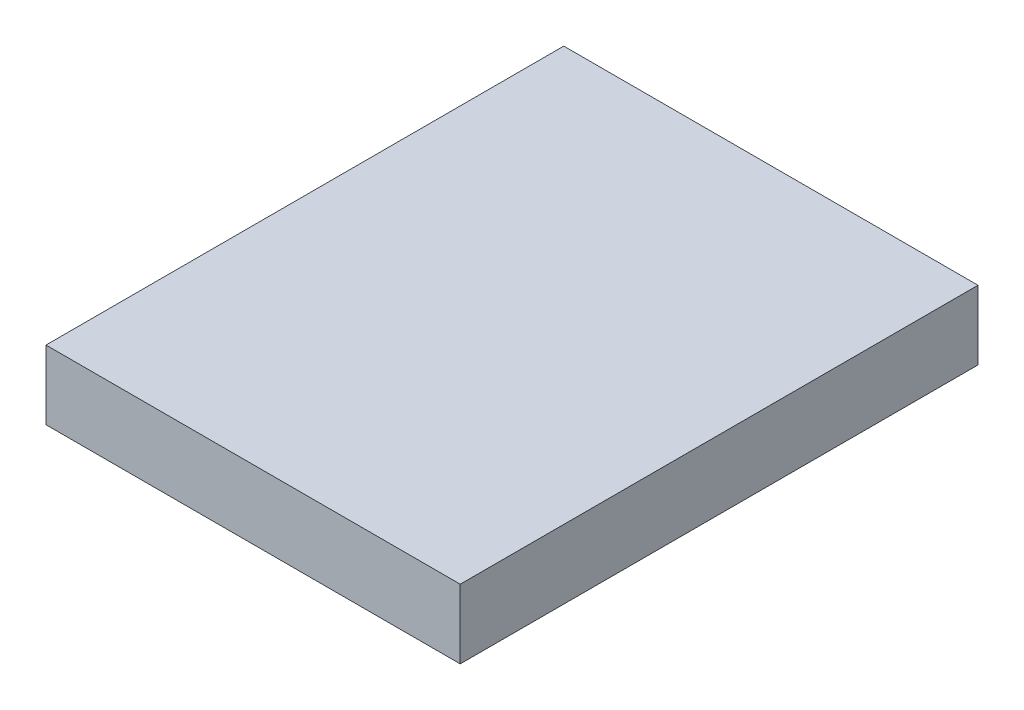
SolidWorks part; units mm, degrees
ref_plane "Front Plane" through (0, 0, 0) normal (0, 0, 1) x (1, 0, 0)
ref_plane "Top Plane" through (0, 0, 0) normal (0, 1, 0) x (1, 0, 0)
ref_plane "Right Plane" through (0, 0, 0) normal (1, 0, 0) x (0, 0, -1)
sketch "Sketch1" plane through (0, 0, 0) normal (0, 1, 0) x (1, 0, 0)
  line L1 (0, 0) -> (229, 0)
  line L2 (0, 0) -> (0, -12.7)
  line L3 (0, -12.7) -> (229, -12.7)
  line L4 (229, 0) -> (229, -12.7)
  dimension "D1" = 229
  dimension "D2" = 12.7
extrude "Boss-Extrude1" add sketch "Sketch1" against normal blind 1
sketch "Sketch2" [suppressed] plane through (0, 0, 0) normal (0, 1, 0) x (1, 0, 0)
  line L0 (229, -12.7) -> (229, 0) construction
  line L1 (0, -12.7) -> (229, -12.7)
  line L2 (0, -12.7) -> (0, -6)
  line L3 (0, -6) -> (229, -6)
  line L4 (229, -12.7) -> (229, -6)
  line L5 (229, 0) -> (0, 0) construction
  dimension "D1" = 6
extrude "Cut-Extrude1" [suppressed] cut sketch "Sketch2" against normal through all
sketch "Sketch3" [suppressed] plane through (0, 0, 0) normal (0, 1, 0) x (1, 0, 0)
  line L0 (229, -12.7) -> (229, 0) construction
  line L1 (0, -12.7) -> (229, -12.7)
  line L2 (0, -12.7) -> (0, -8.5)
  line L3 (0, -8.5) -> (229, -8.5)
  line L4 (229, -12.7) -> (229, -8.5)
  line L5 (229, 0) -> (0, 0) construction
  dimension "D1" = 8.5
extrude "Cut-Extrude2" [suppressed] cut sketch "Sketch3" against normal through all
sketch "Sketch4" plane through (0, 0, 0) normal (0, 1, 0) x (1, 0, 0)
  line L0 (229, 0) -> (0, 0) construction
  line L1 (229, -12.7) -> (6, -12.7)
  line L2 (229, -12.7) -> (229, 0)
  line L3 (229, 0) -> (6, 0)
  line L4 (6, -12.7) -> (6, 0)
  line L5 (0, 0) -> (0, -12.7) construction
  line L7 (6, -12.7) -> (0, -12.7)
  line L8 (6, -12.7) -> (6, -7.5)
  line L9 (6, -7.5) -> (0, -7.5)
  line L10 (0, -12.7) -> (0, -7.5)
  line M4 (0, -12.7) -> (229, -12.7)
  line M5 (229, -12.7) -> (229, 0)
  line M6 (229, 0) -> (0, 0)
  dimension "D1" = 6
  dimension "D2" = 7.5
extrude "Cut-Extrude3" cut sketch "Sketch4" against normal through all contours L4 M4 M5 M6 | L7 L10 L9 L8
sketch "Sketch5" [suppressed] plane through (0, 0, 0) normal (0, 1, 0) x (1, 0, 0)
  line L0 (228.6, 0) -> (0, 0) construction
  line L1 (228.6, -12.7) -> (9.3, -12.7)
  line L2 (228.6, -12.7) -> (228.6, 0)
  line L3 (228.6, 0) -> (9.3, 0)
  line L4 (9.3, -12.7) -> (9.3, 0)
  line L6 (0, -12.7) -> (9.3, -12.7)
  line L7 (0, -12.7) -> (0, -9.3)
  line L8 (0, -9.3) -> (9.3, -9.3)
  line L9 (9.3, -12.7) -> (9.3, -9.3)
  dimension "D1" = 9.3
  dimension "D2" = 9.3
extrude "Cut-Extrude4" [suppressed] cut sketch "Sketch5" against normal through all
sketch "Sketch6" [suppressed] plane through (0, -0.8, 0) normal (0, -1, 0) x (1, 0, 0)
  line L0 (0, 12.7) -> (228.6, 12.7) construction
  line L1 (228.6, 0) -> (9.3, 0)
  line L2 (228.6, 0) -> (228.6, 12.7)
  line L3 (228.6, 12.7) -> (9.3, 12.7)
  line L4 (9.3, 0) -> (9.3, 12.7)
  line L5 (228.6, 0) -> (0, 0) construction
  line L6 (0, 12.7) -> (9.3, 12.7)
  line L7 (0, 12.7) -> (0, 6.2)
  line L8 (0, 6.2) -> (9.3, 6.2)
  line L9 (9.3, 12.7) -> (9.3, 6.2)
  dimension "D1" = 9.3
  dimension "D2" = 6.2
extrude "Cut-Extrude5" [suppressed] cut sketch "Sketch6" against normal through all
sketch "Sketch7" [suppressed] plane through (0, -0.8, 0) normal (0, -1, 0) x (1, 0, 0)
  line L0 (0, 12.7) -> (228.6, 12.7) construction
  line L1 (228.6, 0) -> (8.5, 0)
  line L2 (228.6, 0) -> (228.6, 12.7)
  line L3 (228.6, 12.7) -> (8.5, 12.7)
  line L4 (8.5, 0) -> (8.5, 12.7)
  line L6 (0, 12.7) -> (8.5, 12.7)
  line L7 (0, 12.7) -> (0, 6.2)
  line L8 (0, 6.2) -> (8.5, 6.2)
  line L9 (8.5, 12.7) -> (8.5, 6.2)
  line L10 (228.6, 0) -> (0, 0) construction
  dimension "D1" = 8.5
  dimension "D2" = 6.2
extrude "Cut-Extrude6" [suppressed] cut sketch "Sketch7" against normal through all
